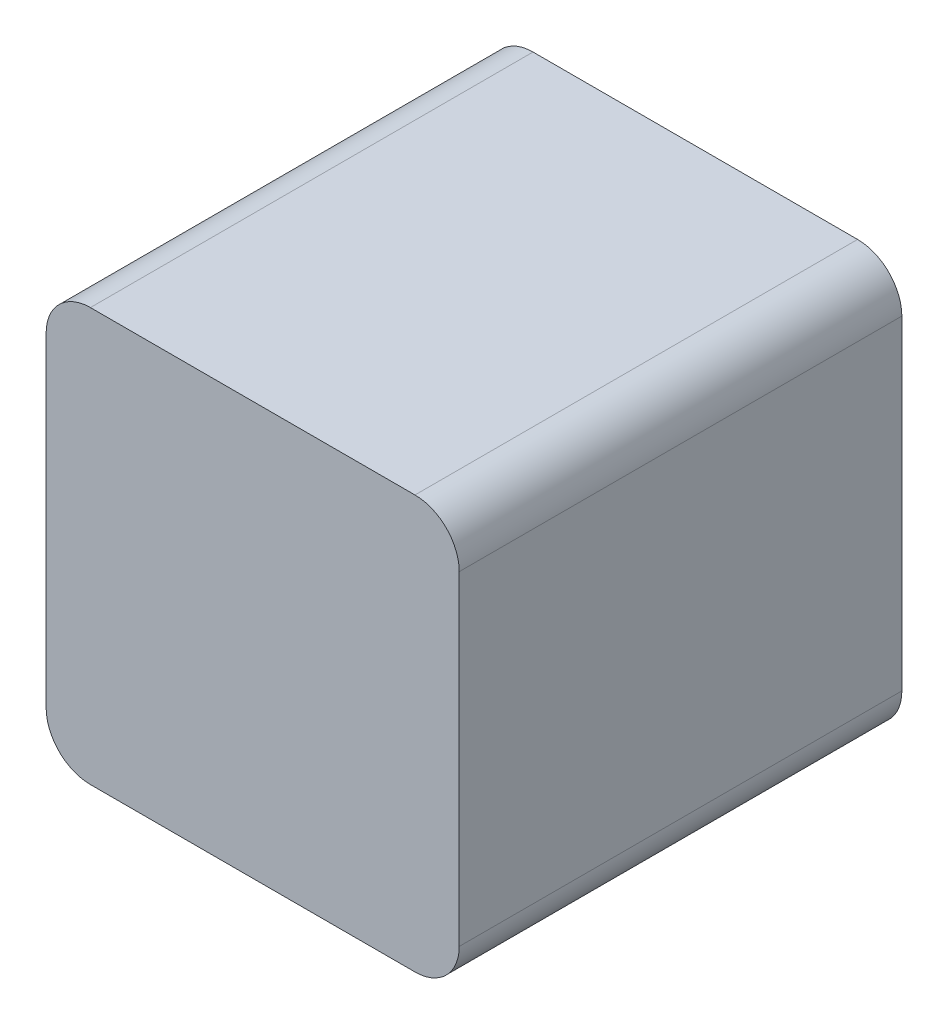
SolidWorks part; units mm, degrees
material "1060 Alloy"
ref_plane "Front Plane" through (0, 0, 0) normal (0, 0, 1) x (1, 0, 0)
ref_plane "Top Plane" through (0, 0, 0) normal (0, 1, 0) x (1, 0, 0)
ref_plane "Right Plane" through (0, 0, 0) normal (1, 0, 0) x (0, 0, -1)
sketch "Sketch1" plane through (0, 0, 0) normal (0, 0, 1) x (1, 0, 0)
  line L1 (-14, 14) -> (14, 14)
  line L2 (-14, 14) -> (-14, -14)
  line L3 (-14, -14) -> (14, -14)
  line L4 (14, 14) -> (14, -14)
  line L5 (-14, 14) -> (14, -14) construction
  line L6 (-14, -14) -> (14, 14) construction
  point P0 (0, 0)
  dimension "D1" = 28
extrude "Boss-Extrude1" add sketch "Sketch1" along normal mid plane 30
sketch "Sketch2" plane through (0, -14, 0) normal (0, -1, 0) x (1, 0, 0)
  line L0 (-14, -15) -> (14, -15) construction
  line L1 (-7.5, -8) -> (7.5, -8)
  line L2 (-7.5, -8) -> (-7.5, -15)
  line L3 (-7.5, -15) -> (7.5, -15)
  line L4 (7.5, -8) -> (7.5, -15)
  point P6 (0, -8)
  dimension "D1" = 15
  dimension "D2" = 7
extrude "Boss-Extrude2" add sketch "Sketch2" along normal mid plane 3
fillet "Fillet1" radius 3 4 edges at (14, -14, 0) (-14, -14, 0) (-14, 14, 0) (14, 14, 0)
